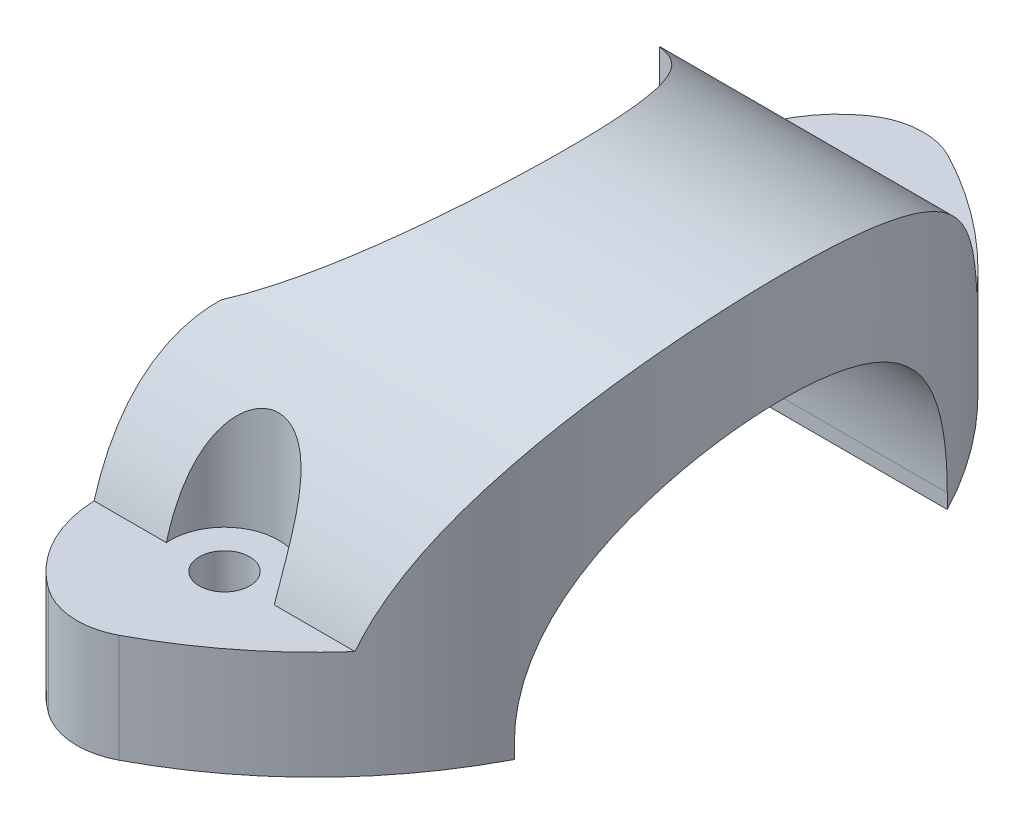
SolidWorks part; units mm, degrees
material "6061-T6 (SS)"
ref_plane "Front Plane" through (0, 0, 0) normal (0, 0, 1) x (1, 0, 0)
ref_plane "Top Plane" through (0, 0, 0) normal (0, 1, 0) x (1, 0, 0)
ref_plane "Right Plane" through (0, 0, 0) normal (1, 0, 0) x (0, 0, -1)
sketch "Sketch1" plane through (0, 0, 0) normal (0, 1, 0) x (1, 0, 0)
  arc A0 (38.5506, -72.9956) -> (38.5506, 72.9956) centre (0, 0) ccw
  arc A1 (22.0628, -38.588) -> (22.0628, 38.588) centre (0, 0) ccw
  circle A2 centre (38.1, 53.975) radius 4.7625
  circle A3 centre (38.1, -53.975) radius 4.445
  arc A4 (25.3126, 72.1528) -> (22.0628, 38.588) centre (38.1, 53.975) ccw
  arc A5 (22.0628, -38.588) -> (25.3126, -72.1528) centre (38.1, -53.975) ccw
  arc A6 (25.3126, -72.1528) -> (38.5506, -72.9956) centre (32.6197, -61.7655) ccw
  arc A7 (25.3126, 72.1528) -> (38.5506, 72.9956) centre (32.6197, 61.7655) cw
  dimension "D1" = 165.1
  dimension "D2" = 88.9
  dimension "D5" = 8.89
  dimension "D6" = 9.525
  dimension "D8" = 44.45
  dimension "D9" = 44.45
  dimension "D10" = 12.7
  dimension "D3" = 53.975
  dimension "D4" = 38.1
  dimension "D7" = 53.975
extrude "Boss-Extrude1" add sketch "Sketch1" along normal blind 76.2
ref_plane "Plane2" through (22.0628, 0, 0) normal (-1, 0, 0) x (0, 0, 1)
sketch "Sketch7" plane through (22.0628, 0, 0) normal (-1, 0, 0) x (0, 0, 1)
  line L0 (-38.1, 2.54) -> (-38.1, 0)
  line L1 (-38.1, 0) -> (38.1, 0)
  line L2 (38.1, 0) -> (38.1, 2.54)
  line L3 (-38.588, 0) -> (38.588, 0) construction
  arc A0 (38.1, 2.54) -> (-38.1, 2.54) centre (0, 2.54) ccw
  dimension "D1" = 76.2
  dimension "D2" = 2.54
extrude "Cut-Extrude6" cut sketch "Sketch7" against normal through all
sketch "Sketch9" plane through (22.0628, 0, 0) normal (-1, 0, 0) x (0, 0, 1)
  line L0 (-74.4655, 76.2) -> (-74.4655, 19.05)
  line L1 (-74.4655, 76.2) -> (-74.4655, 0) construction
  line L2 (-74.4655, 19.05) -> (-54.7133, 19.05)
  line L6 (54.7133, 19.05) -> (74.4655, 19.05)
  line L7 (74.4655, 0) -> (74.4655, 76.2) construction
  line L8 (74.4655, 19.05) -> (74.4655, 76.2)
  line L9 (74.4655, 76.2) -> (-74.4655, 76.2)
  line L10 (-72.1528, 0) -> (-38.588, 0) construction
  arc A1 (-54.7133, 19.05) -> (54.7133, 19.05) centre (0, 2.54) cw
  point P7 (0, 10.0747)
  point P8 (0, 4.433)
  point P15 (0, 0)
  point P16 (0, 0)
  point P19 (63.8894, 19.05)
  point P20 (-52.9411, 19.05)
  point P21 (-59.6331, 19.05)
  point P22 (0, 0)
  dimension "D2" = 57.15
  dimension "D1" = 2.54
  dimension "D3" = 19.05
extrude "Cut-Extrude7" cut sketch "Sketch9" against normal through all both and the other way through all
sketch "Sketch10" plane through (0, 19.05, 0) normal (0, 1, 0) x (1, 0, 0)
  circle A0 centre (38.1, 53.975) radius 9.525
  circle A1 centre (38.1, -53.975) radius 9.525
  dimension "D1" = 19.05
  dimension "D2" = 19.05
extrude "Cut-Extrude8" cut sketch "Sketch10" along normal through all
